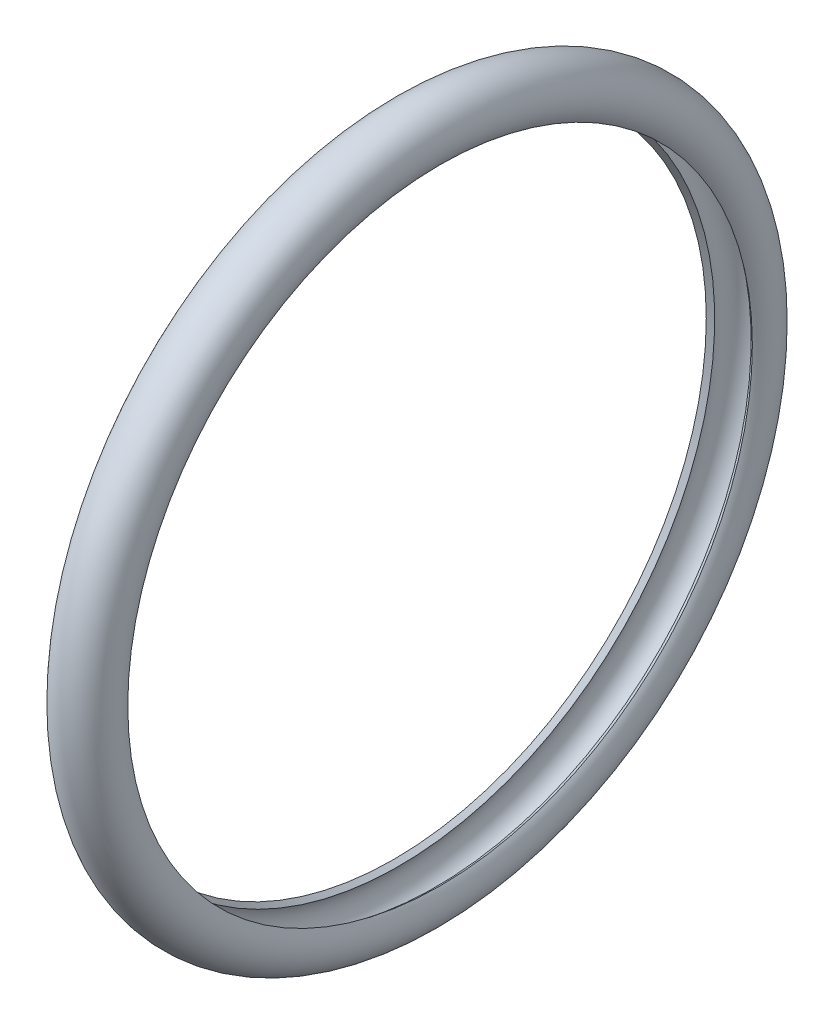
SolidWorks part; units mm, degrees
material "Duranickel(R) 301"
ref_plane "Front Plane" through (0, 0, 0) normal (0, 0, 1) x (1, 0, 0)
ref_plane "Top Plane" through (0, 0, 0) normal (0, 1, 0) x (1, 0, 0)
ref_plane "Right Plane" through (0, 0, 0) normal (1, 0, 0) x (0, 0, -1)
ref_axis "Axis1" through (-88.99, 0, 0) along (1, 0, 0)
sketch "Sketch1" plane through (0, 0, 0) normal (0, 0, 1) x (1, 0, 0)
  line L0 (-88.99, 0) -> (88.99, 0) construction
  line L1 (0.8922, 15) -> (3.2822, 15) construction
  line L2 (0.8922, 15) -> (0.8922, 12.97) construction
  line L3 (0.8922, 12.97) -> (3.2822, 12.97) construction
  line L4 (3.2822, 15) -> (3.2822, 12.97) construction
  line L5 (1.1297, 12.97) -> (1.33, 13.1196)
  line L6 (3.0447, 12.97) -> (2.8444, 13.1196)
  line L7 (1.1297, 12.97) -> (3.0447, 12.97) construction
  line L8 (0.8922, 14.88) -> (3.2822, 14.88) construction
  arc A0 (3.0447, 12.97) -> (1.1297, 12.97) centre (2.0872, 13.685) ccw
  arc A1 (1.33, 13.1196) -> (2.8444, 13.1196) centre (2.0872, 13.685) cw
  dimension "D1" = 2.39
  dimension "D3" = 30
  dimension "D4" = 0.25
  dimension "D5" = 0.12
  dimension "D6" = 0
  dimension "D2" = 1.91
revolve "Revolve1" add sketch "Sketch1" angle 360 about axis through (-88.99, 0, 0) along (1, 0, 0)
equation "\"DG\"= 30mm"
equation "\"AS\"= 2.39mm"
equation "\"RS\"= 1.91mm"
equation "\"D1@Sketch1\"=\"AS\""
equation "\"D3@Sketch1\"=\"DG\""
equation "\"D2@Sketch1\"=\"RS\""
